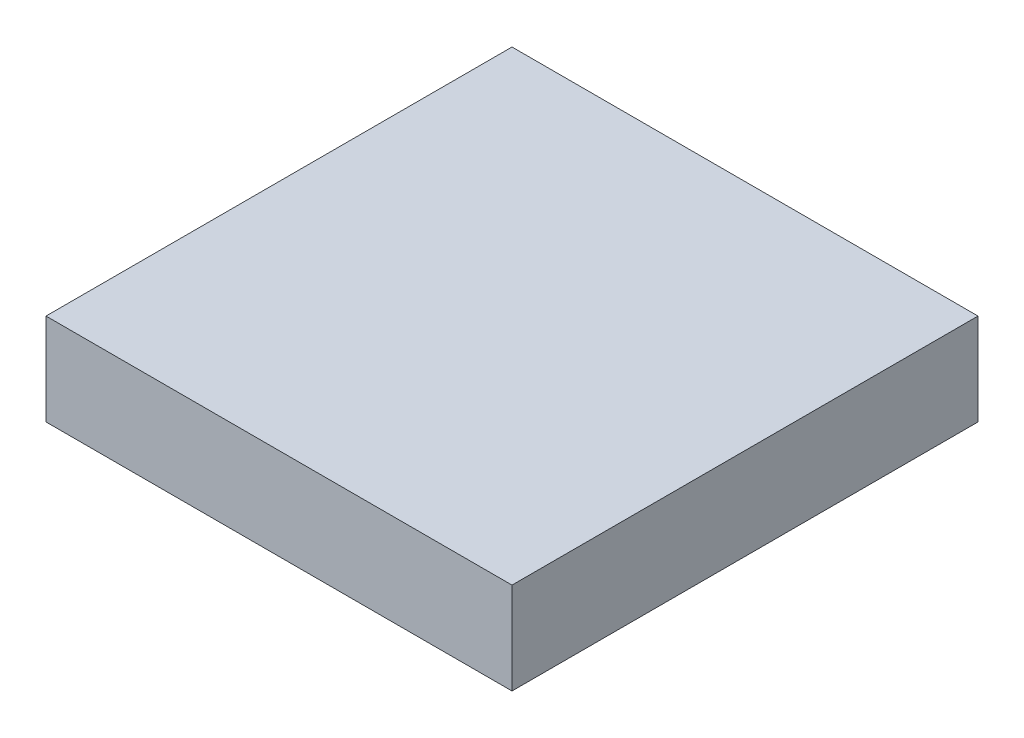
SolidWorks part; units mm, degrees
material "AISI 1020"
ref_plane "Front Plane" through (0, 0, 0) normal (0, 0, 1) x (1, 0, 0)
ref_plane "Top Plane" through (0, 0, 0) normal (0, 1, 0) x (1, 0, 0)
ref_plane "Right Plane" through (0, 0, 0) normal (1, 0, 0) x (0, 0, -1)
sketch "Sketch1" plane through (0, 0, 0) normal (0, 1, 0) x (1, 0, 0)
  line L1 (-76.2, -76.2) -> (76.2, -76.2)
  line L2 (-76.2, -76.2) -> (-76.2, 76.2)
  line L3 (-76.2, 76.2) -> (76.2, 76.2)
  line L4 (76.2, -76.2) -> (76.2, 76.2)
  line L5 (0, 76.2) -> (0, -76.2) construction
  line L6 (-76.2, 0) -> (76.2, 0) construction
  point P0 (0, 0)
  dimension "D1" = 152.4
  dimension "D2" = 152.4
extrude "Boss-Extrude1" add sketch "Sketch1" along normal blind 30
